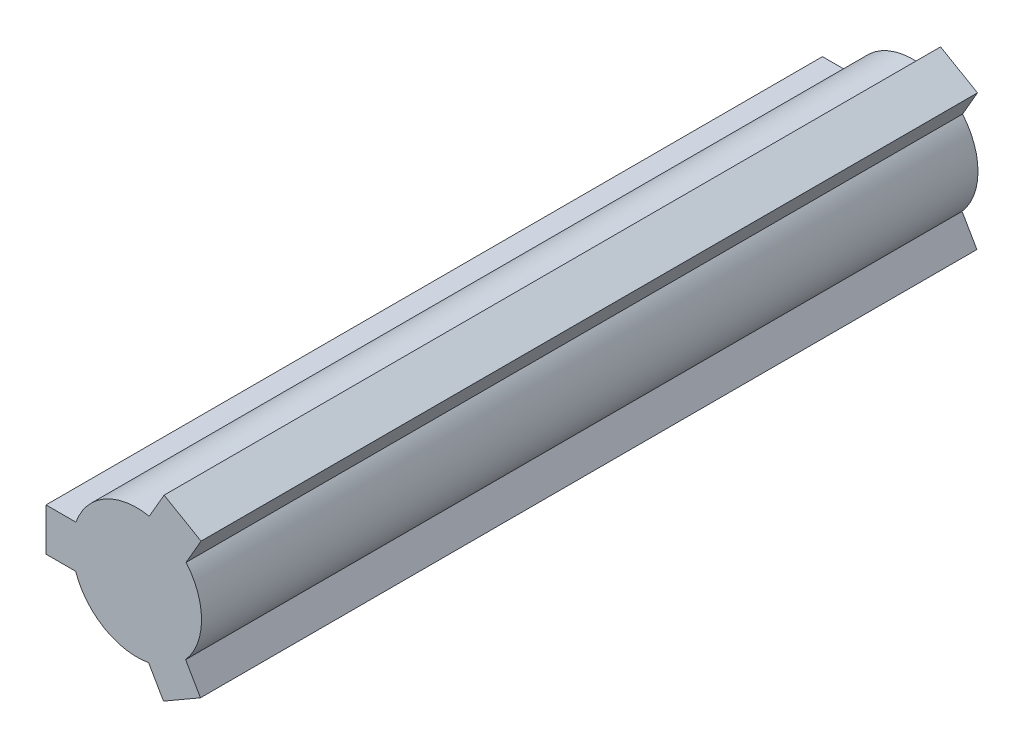
SolidWorks part; units mm, degrees
ref_plane "Front Plane" through (0, 0, 0) normal (0, 0, 1) x (1, 0, 0)
ref_plane "Top Plane" through (0, 0, 0) normal (0, 1, 0) x (1, 0, 0)
ref_plane "Right Plane" through (0, 0, 0) normal (1, 0, 0) x (0, 0, -1)
ref_plane "Plane4"
sketch "Sketch1" plane through (0, 0, 0) normal (0, 0, 1) x (1, 0, 0)
  line L0 (2.417, 2.0589) -> (3.1501, 3.3288)
  line L1 (3.1501, 3.3288) -> (1.3369, 4.3757)
  line L2 (1.3369, 4.3757) -> (0.6096, 3.1159)
  line L3 (-2.9915, 1.0637) -> (-4.4579, 1.0637)
  line L4 (-4.4579, 1.0637) -> (-4.4579, -1.03)
  line L5 (-4.4579, -1.03) -> (-3.0033, -1.03)
  line L6 (0.5745, -3.1226) -> (1.3077, -4.3925)
  line L7 (1.3077, -4.3925) -> (3.121, -3.3456)
  line L8 (3.121, -3.3456) -> (2.3937, -2.0859)
  arc A0 (0.6096, 3.1159) -> (-2.9915, 1.0637) centre (0, 0) ccw
  arc A1 (-3.0033, -1.03) -> (0.5745, -3.1226) centre (0, 0) ccw
  arc A2 (2.3937, -2.0859) -> (2.417, 2.0589) centre (0, 0) ccw
extrude "Extrusion1" add sketch "Sketch1" along normal blind 38.1
